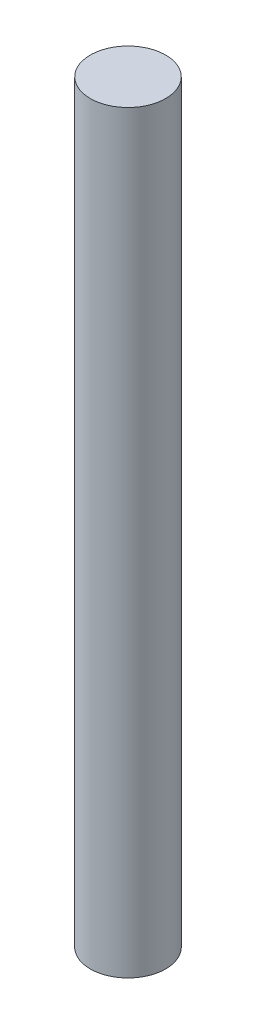
SolidWorks part; units mm, degrees
ref_plane "Спереди" through (0, 0, 0) normal (0, 0, 1) x (1, 0, 0)
ref_plane "Сверху" through (0, 0, 0) normal (0, 1, 0) x (1, 0, 0)
ref_plane "Справа" through (0, 0, 0) normal (1, 0, 0) x (0, 0, -1)
other "Configuration Table"
sketch "Эскиз1" plane through (0, 0, 0) normal (0, 1, 0) x (1, 0, 0)
  circle A0 centre (-3.3478, 1.9239) radius 2.5
  dimension "D1" = 5
extrude "Бобышка-Вытянуть1" add sketch "Эскиз1" along normal blind 50
